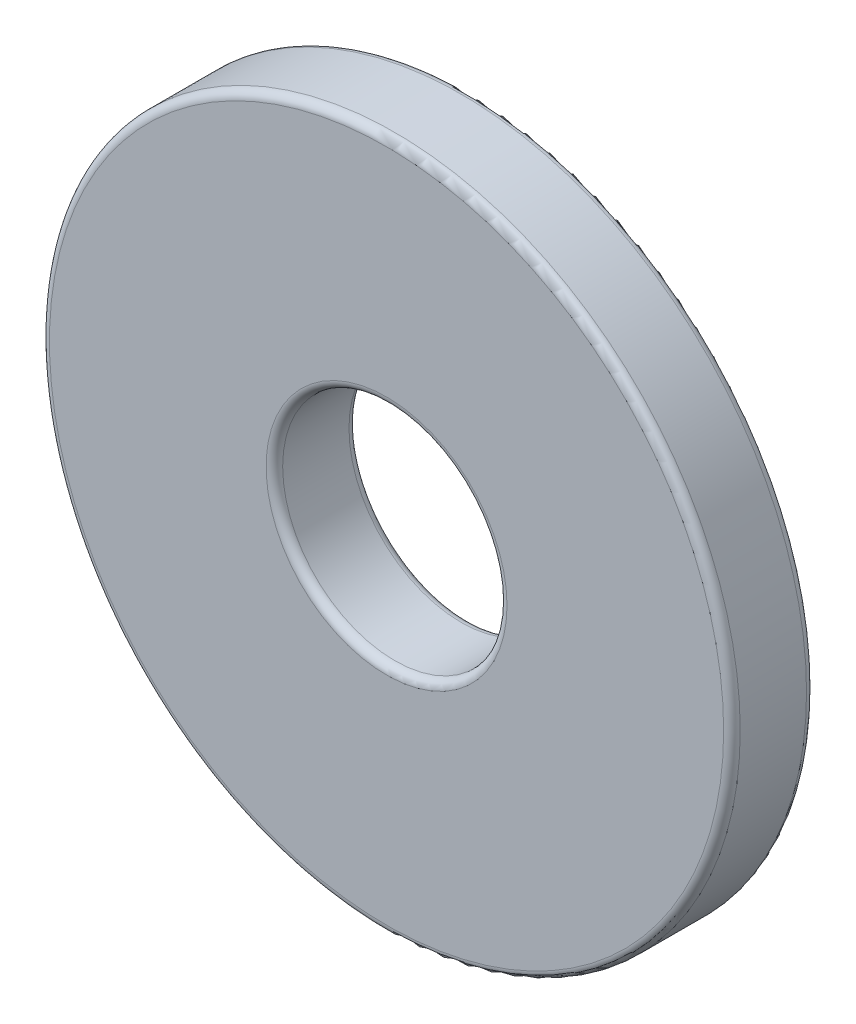
SolidWorks part; units mm, degrees
ref_plane "Front Plane" through (0, 0, 0) normal (0, 0, 1) x (1, 0, 0)
ref_plane "Top Plane" through (0, 0, 0) normal (0, 1, 0) x (1, 0, 0)
ref_plane "Right Plane" through (0, 0, 0) normal (1, 0, 0) x (0, 0, -1)
sketch "Sketch1" plane through (0, 0, 0) normal (0, 0, 1) x (1, 0, 0)
  circle A0 centre (0, 0) radius 2.5781
  circle A1 centre (0, 0) radius 7.9375
  point P4 (0, 7.9375)
  point P5 (0, 2.5781)
  point P6 (0, -2.5781)
  point P7 (2.5781, 0)
  point P8 (-2.5781, 0)
  dimension "OD" = 15.875
  dimension "ID" = 5.1562
sketch "Sketch2" plane through (0, 0, 0) normal (1, 0, 0) x (0, 0, -1)
  line L1 (-0.9525, 7.9375) -> (0.9525, 7.9375)
  line L2 (-0.9525, 7.9375) -> (-0.9525, -7.9375)
  line L3 (-0.9525, -7.9375) -> (0.9525, -7.9375)
  line L4 (0.9525, 7.9375) -> (0.9525, -7.9375)
  point P4 (0, 7.9375)
  point P5 (0.9525, 0)
  dimension "Thickness" = 1.905
sketch "Sketch3" plane through (0, 0, 0) normal (0, 0, 1) x (1, 0, 0)
  circle A0 centre (0, 0) radius 2.5781 construction
  circle A1 centre (0, 0) radius 7.9375 construction
  circle A2 centre (0, 0) radius 2.5781
  circle A3 centre (0, 0) radius 7.9375
extrude "Boss-Extrude1" add sketch "Sketch3" against normal up to vertex (0.9525 mm away) from vertex at 0.9525 starting at point (0, 7.9375, 0.9525)
fillet "Fillet1" radius 0.1905 4 edges at (2.5781, 0, 0.9525) (2.5781, 0, -0.9525) (7.9375, 0, 0.9525) (7.9375, 0, -0.9525)
equation "\"D1@Fillet1\"=\"Thickness@Sketch2\"*.1"
